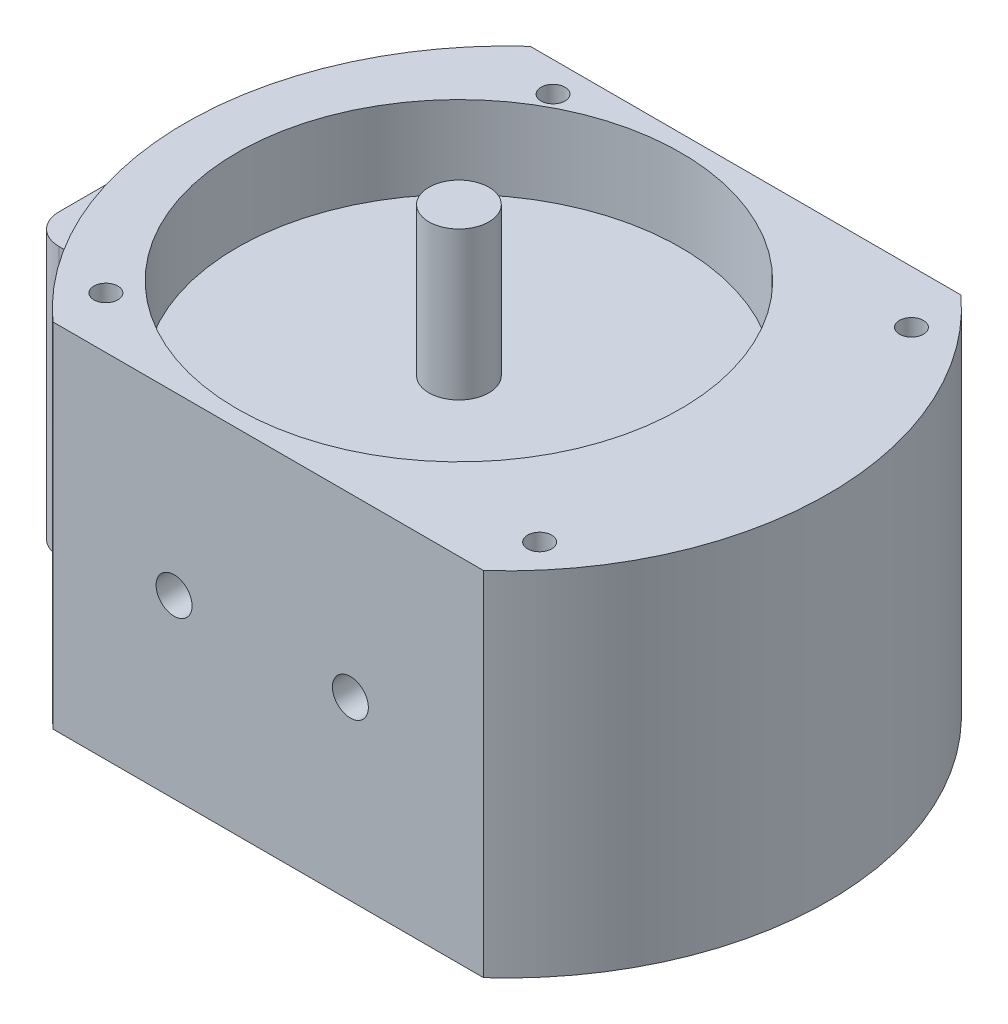
SolidWorks part; units mm, degrees
material "ABS"
ref_plane "Front Plane" through (0, 0, 0) normal (0, 0, 1) x (1, 0, 0)
ref_plane "Top Plane" through (0, 0, 0) normal (0, 1, 0) x (1, 0, 0)
ref_plane "Right Plane" through (0, 0, 0) normal (1, 0, 0) x (0, 0, -1)
sketch "Sketch1" plane through (0, 0, 0) normal (0, 1, 0) x (1, 0, 0)
  line L0 (-21.395, 0) -> (21.395, 0) construction
  line L2 (-13.9508, 19.9) -> (21.9508, 19.9)
  line L5 (-26.15, 16.5) -> (-17.1185, 16.5)
  line L6 (-28.65, 14) -> (-28.65, -4.7)
  line L7 (-26.15, -7.2) -> (-21.8147, -7.2)
  line L9 (-28.65, 16.5) -> (-27.953, 15.7319) construction
  line L10 (-28.65, -7.2) -> (-27.953, -6.4319) construction
  line L11 (-13.9508, -19.9) -> (21.9508, -19.9)
  arc A0 (21.9508, -19.9) -> (21.9508, 19.9) centre (4, 0) ccw
  arc A1 (-26.15, -7.2) -> (-28.65, -4.7) centre (-26.15, -4.7) cw
  arc A2 (-26.15, 16.5) -> (-28.65, 14) centre (-26.15, 14) ccw
  arc A3 (-13.9508, 19.9) -> (-17.1185, 16.5) centre (4, 0) ccw
  arc A4 (-21.8147, -7.2) -> (-13.9508, -19.9) centre (4, 0) ccw
  dimension "D1" = 53.6
  dimension "D9" = 2.5
  dimension "D2" = 19.9
  dimension "D6" = 23.7
  dimension "D7" = 3.4
  dimension "D8" = 28.65
extrude "Boss-Extrude1" add sketch "Sketch1" along normal blind 29.4
sketch "Sketch2" plane through (0, 29.4, 0) normal (0, 1, 0) x (1, 0, 0)
  circle A0 centre (0, 0) radius 18.5
  dimension "D1" = 37
extrude "Cut-Extrude1" cut sketch "Sketch2" against normal blind 6.85
sketch "Sketch3" plane through (0, 22.55, 0) normal (0, 1, 0) x (1, 0, 0)
  circle A0 centre (0, 0) radius 2.5
  dimension "D1" = 5
extrude "Boss-Extrude2" add sketch "Sketch3" along normal blind 12.35
sketch "Sketch4" plane through (0, 0, 0) normal (0, -1, 0) x (1, 0, 0)
  circle A0 centre (0, 0) radius 2.85
  dimension "D1" = 5.7
extrude "Boss-Extrude3" add sketch "Sketch4" along normal blind 4
sketch "Sketch5" plane through (0, 29.4, 0) normal (0, 1, 0) x (1, 0, 0)
  line L0 (0, -21.395) -> (0, 21.395) construction
  line L2 (-29.9932, 17.4001) -> (-16.3832, 17.4001)
  line L3 (-29.9932, 17.4001) -> (-29.9932, -7.8658)
  line L4 (-29.9932, -7.8658) -> (-21.6197, -7.8658)
  line L6 (-29.9932, 17.4001) -> (-22.2441, 4.7672) construction
  line L7 (-29.9932, -7.8658) -> (-22.2441, 4.7672) construction
  arc A0 (-16.3832, 17.4001) -> (-21.6197, -7.8658) centre (4, 0) ccw
  point P4 (-22.2441, 4.7672)
  dimension "D1" = 53.6
  dimension "D2" = 4
extrude "Cut-Extrude3" cut sketch "Sketch5" against normal blind 7
sketch "Sketch6" plane through (0, 0, 19.9) normal (0, 0, 1) x (1, 0, 0)
  line L0 (-2.35, 29.4) -> (-2.35, 0) construction
  line L1 (-13.9508, 29.4) -> (21.9508, 29.4) construction
  line L2 (-2.85, 0) -> (2.85, 0) construction
  line L3 (-28.65, 22.4) -> (-28.65, 0) construction
  circle A0 centre (-3.85, 14.7) radius 1.5
  circle A1 centre (10.85, 14.7) radius 1.5
  point P13 (-2.35, 14.7)
  dimension "D1" = 3
  dimension "D5" = 3
  dimension "D2" = 26.3
  dimension "D3" = 1.5
  dimension "D4" = 0
extrude "Cut-Extrude4" cut sketch "Sketch6" against normal through all
sketch "Sketch7" plane through (0, 0, 0) normal (0, -1, 0) x (1, 0, 0)
  line L0 (0, 0) -> (-9.5531, -17.4) construction
  line L1 (0, 0) -> (22.2297, -15.5) construction
  line L2 (0, 0) -> (22.2297, 15.5) construction
  line L3 (22.2297, -15.5) -> (22.2297, 15.5) construction
  line L4 (21.9508, -19.9) -> (-13.9508, -19.9) construction
  line L5 (0, 0) -> (-13.8334, 15.6) construction
  line L6 (-13.9508, 19.9) -> (21.9508, 19.9) construction
  circle A3 centre (-13.8334, 15.6) radius 1
  circle A4 centre (-9.5531, -17.4) radius 1
  circle A5 centre (22.2297, -15.5) radius 1
  circle A6 centre (22.2297, 15.5) radius 1
  dimension "D9" = 2
  dimension "D10" = 2
  dimension "D11" = 2
  dimension "D12" = 2
  dimension "D1" = 19.85
  dimension "D3" = 27.1
  dimension "D4" = 31
  dimension "D6" = 2.5
  dimension "D7" = 20.85
  dimension "D8" = 4.3
extrude "Cut-Extrude5" cut sketch "Sketch7" against normal through all contours A3 | A6 | A5 | A4
equation "\"D2@Sketch1\"=0.0398/2"
equation "\"D5@Sketch6\"=\"D1@Sketch6\""
equation "\"D3@Sketch7\"=\"D2@Sketch7\""
equation "\"D7@Sketch7\"=0.018 +(0.0057/2)"
equation "\"D10@Sketch7\"=\"D9@Sketch7\""
equation "\"D11@Sketch7\"=\"D9@Sketch7\""
equation "\"D12@Sketch7\"=\"D9@Sketch7\""
